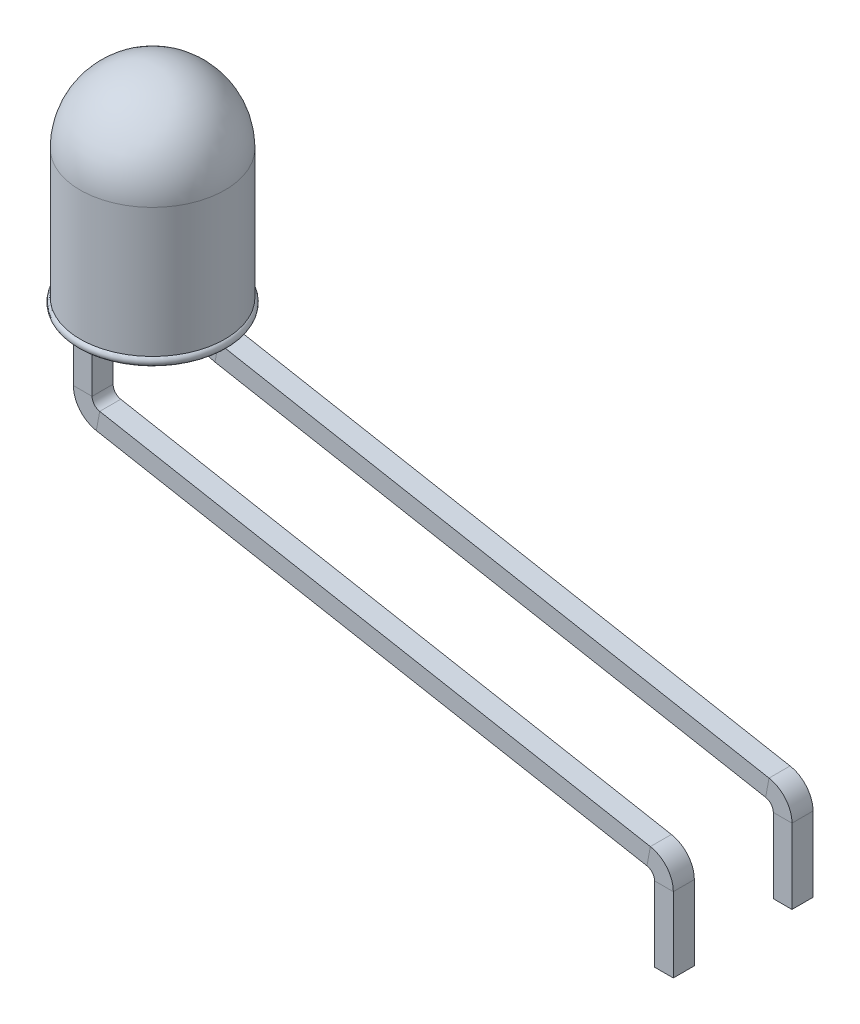
SolidWorks part; units mm, degrees
ref_plane "Front Plane" through (0, 0, 0) normal (0, 0, 1) x (1, 0, 0)
ref_plane "Top Plane" through (0, 0, 0) normal (0, 1, 0) x (1, 0, 0)
ref_plane "Right Plane" through (0, 0, 0) normal (1, 0, 0) x (0, 0, -1)
sketch "Sketch1" plane through (0, 0, 0) normal (0, 0, 1) x (1, 0, 0)
  line L0 (0, 0) -> (-1.5, 0)
  line L1 (-1.55, 0.1866) -> (-1.55, 2.95)
  line L2 (0, 4.5) -> (0, 0) construction
  line L3 (-0.5895, 4.5) -> (0, 4.5) construction
  line L4 (-1.6, 0) -> (-1.6, 1.9354) construction
  line L5 (0, 4.5) -> (0, 0)
  arc A0 (-1.5, 0) -> (-1.55, 0.1866) centre (-1.5, 0.1) cw
  arc A1 (-1.55, 2.95) -> (0, 4.5) centre (0, 2.95) cw
  dimension "D3" = 0.1
  dimension "D1" = 1.6
  dimension "D2" = 0.05
  dimension "D4" = 4.5
revolve "Revolve1" add sketch "Sketch1" angle 360 about L5
sketch "Sketch2" plane through (0, 0, 0) normal (0, -1, 0) x (1, 0, 0)
  line L0 (0, 1.045) -> (0, -1.045) construction
  line L1 (-0.2, 1.495) -> (0.2, 1.495)
  line L2 (-0.2, 1.495) -> (-0.2, 1.045)
  line L3 (-0.2, 1.045) -> (0.2, 1.045)
  line L4 (0.2, 1.495) -> (0.2, 1.045)
  line L5 (-0.2, -1.045) -> (0.2, -1.045)
  line L6 (-0.2, -1.045) -> (-0.2, -1.495)
  line L7 (-0.2, -1.495) -> (0.2, -1.495)
  line L8 (0.2, -1.045) -> (0.2, -1.495)
  point P10 (0, 0)
  point P13 (0.2, -1.27)
  point P15 (0.2, 1.27)
  dimension "D1" = 0.45
  dimension "D2" = 0.4
  dimension "D3" = 2.54
sketch "Sketch4" plane through (0, 0, 0) normal (0, 0, 1) x (1, 0, 0)
  line L0 (0, 0) -> (0, -0.8)
  line L1 (-1.5, 0) -> (1.5, 0) construction
  line L2 (0.3274, -1.1934) -> (12.1126, -3.3679)
  line L3 (12.44, -3.7613) -> (12.44, -5.3613)
  arc A0 (12.1126, -3.3679) -> (12.44, -3.7613) centre (12.04, -3.7613) cw
  arc A1 (0, -0.8) -> (0.3274, -1.1934) centre (0.4, -0.8) ccw
  point P0 (12.44, -5.3613)
  point P17 (12.44, -3.4284)
  point P20 (0, -1.1329)
  dimension "D4" = 0.4
  dimension "D1" = 12.44
  dimension "D2" = 1.6
  dimension "D3" = 12.65
  dimension "D5" = 0.8
sketch "Sketch3" plane through (0, 0, 0) normal (0, -1, 0) x (1, 0, 0)
  line L1 (1, 0.225) -> (1.4, 0.225)
  line L2 (1, 0.225) -> (1, -0.225)
  line L3 (1, -0.225) -> (1.4, -0.225)
  line L4 (1.4, 0.225) -> (1.4, -0.225)
  line L6 (0, 0) -> (1, 0) construction
  line L7 (-0.2, 1.045) -> (0.2, 1.045) construction
  line L8 (0.2, 1.495) -> (0.2, 1.045) construction
  dimension "D1" = 1
sweep "Sweep1" add profiles "Sketch2" path "Sketch4"
sketch "Sketch6" plane through (0, 0, 0) normal (0, -1, 0) x (1, 0, 0)
  line L0 (-0.2, 1.495) -> (-0.2, 1.045) construction
  line L1 (1, 0.225) -> (1.4, 0.225)
  line L2 (1, 0.225) -> (1, -0.225)
  line L3 (1, -0.225) -> (1.4, -0.225)
  line L4 (1.4, 0.225) -> (1.4, -0.225)
  line L5 (-0.2, 1.045) -> (0.2, 1.045) construction
  line L6 (1, 0) -> (0, 0) construction
  dimension "D1" = 1
sketch "Sketch7" plane through (0, 0, 0) normal (0, 0, 1) x (1, 0, 0)
  line L0 (1.2, 0) -> (1.2, -0.6147)
  line L1 (1, 0) -> (1.4, 0) construction
  line L2 (0.3274, -1.1934) -> (12.1126, -3.3679) construction
  line L3 (1.5274, -1.008) -> (13.6126, -3.238)
  line L4 (13.94, -3.6313) -> (13.94, -5.3613)
  arc A0 (1.2, -0.6147) -> (1.5274, -1.008) centre (1.6, -0.6147) ccw
  arc A1 (13.6126, -3.238) -> (13.94, -3.6313) centre (13.54, -3.6313) cw
  arc A2 (0, -0.8) -> (0.3274, -1.1934) centre (0.4, -0.8) ccw construction
  arc A3 (12.44, -3.7613) -> (12.1126, -3.3679) centre (12.04, -3.7613) ccw construction
  dimension "D1" = 1.5
  dimension "D2" = 0.4
sweep "Sweep2" [suppressed] add profiles "Sketch6" path "Sketch7"
sketch "Sketch8" plane through (0, -5.3613, 0) normal (0, -1, 0) x (-1, 0, 0)
  line L0 (-12.44, 1.045) -> (-12.44, 1.495) construction
  line L1 (-12.64, 1.045) -> (-12.24, 1.045) construction
  line L2 (-12.24, 1.495) -> (-12.64, 1.495) construction
  line L3 (-12.44, -1.495) -> (-12.44, -1.045) construction
  line L4 (-12.64, -1.495) -> (-12.24, -1.495) construction
  line L5 (-12.24, -1.045) -> (-12.64, -1.045) construction
  point P12 (-12.44, -1.27)
  point P13 (-12.44, 1.27)
sketch "Sketch9" [suppressed] plane through (0, -5.3613, 0) normal (0, -1, 0) x (-1, 0, 0)
  line L0 (-13.94, -0.225) -> (-13.94, 0.225) construction
  line L1 (-14.14, -0.225) -> (-13.74, -0.225) construction
  line L2 (-13.74, 0.225) -> (-14.14, 0.225) construction
  line L3 (-12.44, 1.045) -> (-12.44, 1.495) construction
  line L4 (-12.64, 1.045) -> (-12.24, 1.045) construction
  line L5 (-12.24, 1.495) -> (-12.64, 1.495) construction
  line L6 (-12.44, -1.495) -> (-12.44, -1.045) construction
  line L7 (-12.64, -1.495) -> (-12.24, -1.495) construction
  line L8 (-12.24, -1.045) -> (-12.64, -1.045) construction
  point P18 (-13.94, 0)
  point P19 (-12.44, -1.27)
  point P20 (-12.44, 1.27)
